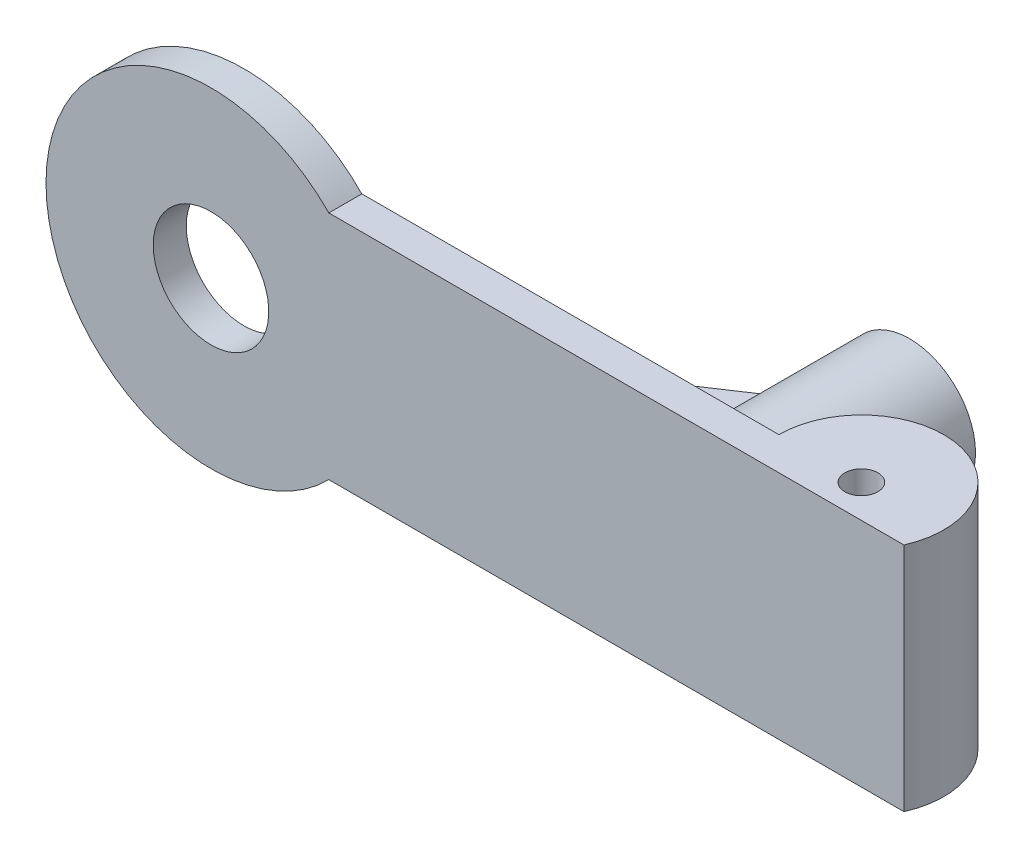
SolidWorks part; units mm, degrees
ref_plane "Front Plane" through (0, 0, 0) normal (0, 0, 1) x (1, 0, 0)
ref_plane "Top Plane" through (0, 0, 0) normal (0, 1, 0) x (1, 0, 0)
ref_plane "Right Plane" through (0, 0, 0) normal (1, 0, 0) x (0, 0, -1)
sketch "Sketch1" plane through (0, 0, 0) normal (0, 1, 0) x (1, 0, 0)
  line L0 (-25, 0) -> (-187.0871, 0)
  line L1 (-187.0871, 0) -> (-187.0871, -10)
  line L2 (-187.0871, -10) -> (22.9129, -10)
  arc A0 (22.9129, -10) -> (-25, 0) centre (0, 0) ccw
  circle A1 centre (0, 0) radius 5
  dimension "D1" = 50
  dimension "D2" = 10
  dimension "D3" = 10
  dimension "D4" = 210
extrude "Boss-Extrude2" add sketch "Sketch1" along normal blind 70
sketch "Sketch3" plane through (0, 0, 0) normal (0, 0, -1) x (-1, 0, 0)
  line L0 (187.0871, 70) -> (187.0871, 0) construction
  line L1 (25, 0) -> (187.0871, 0) construction
  line L2 (25, 70) -> (187.0871, 70) construction
  line L3 (151.38, 0) -> (187.0871, 0)
  line L4 (187.0871, 70) -> (187.0871, 0)
  line L5 (151.38, 70) -> (187.0871, 70)
  circle A0 centre (187.0871, 35) radius 50
  line M1 (25, 0) -> (187.0871, 0)
  line M2 (187.0871, 0) -> (187.0871, 70)
  line M3 (187.0871, 70) -> (25, 70)
  dimension "D1" = 100
extrude "Boss-Extrude3" add sketch "Sketch3" against normal blind 10 contours A0 M3 M1 M2 | A0 M1 M3 M2
sketch "Sketch4" plane through (0, 0, 0) normal (0, 0, -1) x (-1, 0, 0)
  circle A0 centre (187.0871, 35) radius 17.5
  dimension "D1" = 35
extrude "Cut-Extrude1" cut sketch "Sketch4" against normal blind 10
sketch "Sketch5" plane through (0, 0, 0) normal (0, 0, -1) x (-1, 0, 0)
  circle A0 centre (45.4086, 35) radius 20
  circle A1 centre (45.4086, 35) radius 7.5
  dimension "D1" = 40
  dimension "D2" = 15
extrude "Boss-Extrude4" add sketch "Sketch5" along normal blind 60
ref_plane "Plane1" through (0, 35, 0) normal (0, 1, 0) x (1, 0, 0)
sketch "Sketch7" plane through (0, 35, 0) normal (0, 1, 0) x (1, 0, 0)
  line L0 (-65.4086, 40) -> (-65.4086, 0)
  line L1 (-65.4086, 60) -> (-65.4086, 0) construction
  line L2 (-65.4086, 0) -> (-125.4086, 0)
  line L3 (-25, 0) -> (-151.38, 0) construction
  line L4 (-125.4086, 0) -> (-65.4086, 40)
  point P5 (0, 0)
  dimension "D1" = 60
  dimension "D2" = 40
extrude "Boss-Extrude9" add sketch "Sketch7" along normal mid plane 10 separate body
